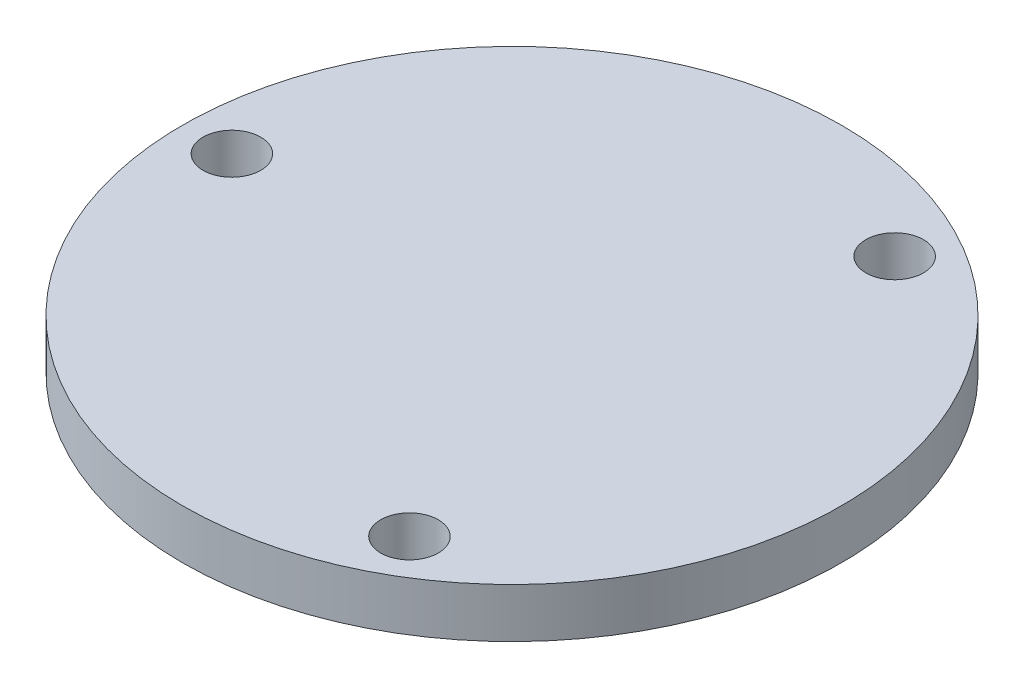
SolidWorks part; units mm, degrees
ref_plane "Front Plane" through (0, 0, 0) normal (0, 0, 1) x (1, 0, 0)
ref_plane "Top Plane" through (0, 0, 0) normal (0, 1, 0) x (1, 0, 0)
ref_plane "Right Plane" through (0, 0, 0) normal (1, 0, 0) x (0, 0, -1)
sketch "Sketch1" plane through (0, -8, 0) normal (0, -1, 0) x (1, 0, 0)
  circle A0 centre (-34.1432, 5.1297) radius 20
  dimension "D1" = 40
extrude "Boss-Extrude1" add sketch "Sketch1" along normal blind 3
sketch "Sketch2" plane through (0, -11, 0) normal (0, -1, 0) x (1, 0, 0)
  line L0 (-54.1432, 5.1297) -> (45.8568, 5.1297) construction
  line L1 (-34.1432, 5.1297) -> (-25.6432, 19.8521) construction
  line L2 (-34.1432, 5.1297) -> (-25.6432, -9.5927) construction
  circle A0 centre (-51.1432, 5.1297) radius 1.75
  circle A1 centre (-25.6432, 19.8521) radius 1.75
  circle A2 centre (-25.6432, -9.5927) radius 1.75
  dimension "D1" = 3.5
  dimension "D2" = 3.5
  dimension "D3" = 3.5
  dimension "D4" = 17
  dimension "D5" = 17
  dimension "D6" = 17
  dimension "D7" = 120
  dimension "D8" = 120
extrude "Cut-Extrude1" cut sketch "Sketch2" against normal up to next
